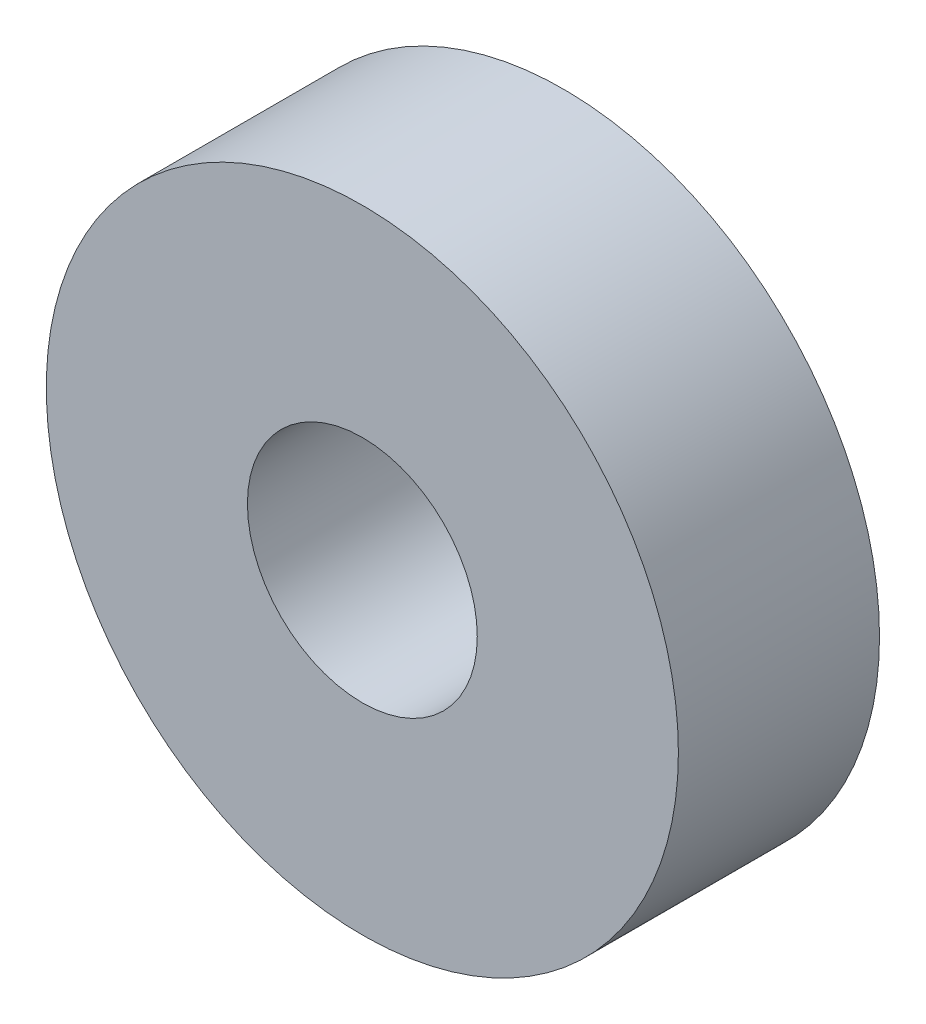
SolidWorks part; units mm, degrees
ref_plane "Front Plane" through (0, 0, 0) normal (0, 0, 1) x (1, 0, 0)
ref_plane "Top Plane" through (0, 0, 0) normal (0, 1, 0) x (1, 0, 0)
ref_plane "Right Plane" through (0, 0, 0) normal (1, 0, 0) x (0, 0, -1)
sketch "Sketch1" plane through (0, 0, 0) normal (0, 0, 1) x (1, 0, 0)
  circle A0 centre (0, 0) radius 4
  circle A1 centre (0, 0) radius 11
  dimension "D1" = 8
  dimension "D2" = 22
extrude "Boss-Extrude1" add sketch "Sketch1" along normal mid plane 7
